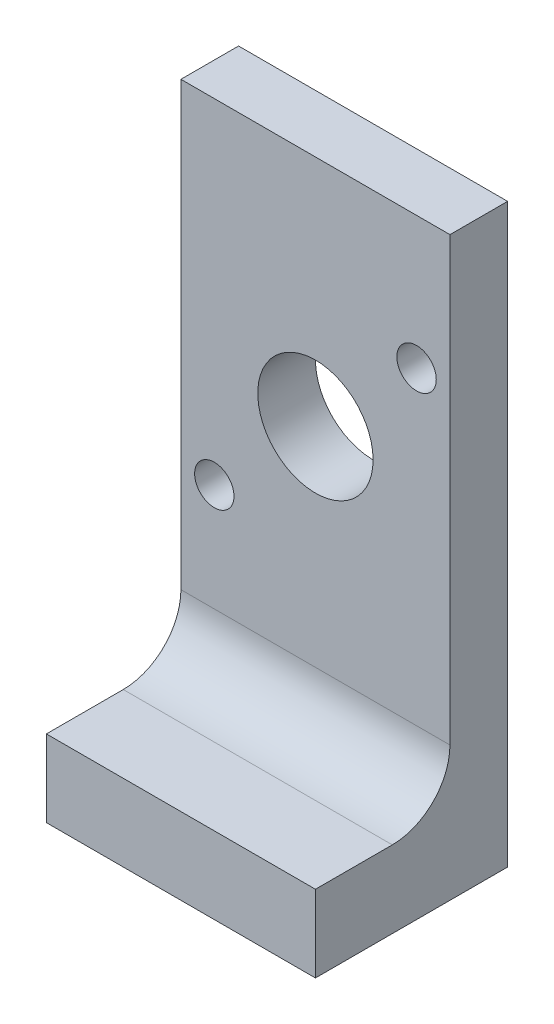
SolidWorks part; units mm, degrees
ref_plane "Front Plane" through (0, 0, 0) normal (0, 0, 1) x (1, 0, 0)
ref_plane "Top Plane" through (0, 0, 0) normal (0, 1, 0) x (1, 0, 0)
ref_plane "Right Plane" through (0, 0, 0) normal (1, 0, 0) x (0, 0, -1)
sketch "Sketch1" plane through (0, 0, 0) normal (1, 0, 0) x (0, 0, -1)
  line L0 (0, 0) -> (10, 0)
  line L1 (10, 0) -> (10, 30)
  line L2 (10, 30) -> (7, 30)
  line L3 (7, 30) -> (7, 7)
  line L4 (4, 4) -> (0, 4)
  line L5 (0, 4) -> (0, 0)
  arc A0 (7, 7) -> (4, 4) centre (4, 7) cw
  dimension "D1" = 3
  dimension "D2" = 4
  dimension "D3" = 3
  dimension "D4" = 10
  dimension "D5" = 30
extrude "Boss-Extrude1" add sketch "Sketch1" along normal blind 14
hole_wizard "Tap Drill for M3x0.5 Tap1" positions "Sketch3" profile "Sketch2" hole size "M3x0.5" standard "ANSI Metric"
sketch "Sketch3" plane through (0, 0, 0) normal (0, -1, 0) x (-1, 0, 0)
  line L0 (-14, 0) -> (0, 0) construction
  line L1 (-14, 10) -> (0, 10) construction
  line L2 (-14, 0) -> (-14, 10) construction
  line L3 (0, 0) -> (0, 10) construction
  point P0 (-11, 7)
  point P2 (-3, 3)
  dimension "D1" = 3
  dimension "D2" = 3
  dimension "D3" = 3
  dimension "D4" = 3
sketch "Sketch2" plane through (11, 0, -7) normal (1, 0, 0) x (0, 0, -1)
  line L0 (0, 0) -> (0, 3.7511)
  line L1 (0, 3.7511) -> (1.25, 3)
  line L2 (1.25, 3) -> (1.25, 0)
  line L5 (1.25, 0) -> (0, 0)
  line L10 (0, 3.7511) -> (-1.25, 3) construction
  line L11 (0, -6.35) -> (0, 107.95) construction
  dimension "Hole Dia." = 2.5
  dimension "Hole Depth" = 3
  dimension "Drill Angle" = 118
sketch "Sketch4" plane through (0, 0, -7) normal (0, 0, 1) x (1, 0, 0)
  line L0 (14, 0) -> (0, 0) construction
  line L1 (0, 30) -> (0, 7) construction
  circle A0 centre (7, 17.85) radius 3
  dimension "D1" = 6
  dimension "D2" = 17.85
  dimension "D3" = 7
extrude "Cut-Extrude1" cut sketch "Sketch4" against normal up to next
hole_wizard "Tap Drill for M2.5x0.45 Tap1" positions "Sketch6" profile "Sketch5" hole size "M2.5x0.45" standard "ANSI Metric" end condition up to next
sketch "Sketch6" plane through (0, 0, -7) normal (0, 0, 1) x (1, 0, 0)
  line L6 (12.2624, 23.1124) -> (7, 17.85) construction
  line L9 (1.7376, 12.5876) -> (7, 17.85) construction
  line L11 (14, 30) -> (0, 30) construction
  point P0 (1.7376, 12.5876)
  point P2 (12.2624, 23.1124)
  dimension "D1" = 14.8844
  dimension "D2" = 45
sketch "Sketch5" plane through (1.7376, 12.5876, -7) normal (1, 0, 0) x (0, -1, 0)
  line L0 (0, 0) -> (0, 3)
  line L1 (0, 3) -> (1.025, 3)
  line L2 (1.025, 3) -> (1.025, 0)
  line L5 (1.025, 0) -> (0, 0)
  line L11 (0, -6.35) -> (0, 107.95) construction
  dimension "Thru Hole Dia." = 2.05
  dimension "Thru Hole Depth" = 3
